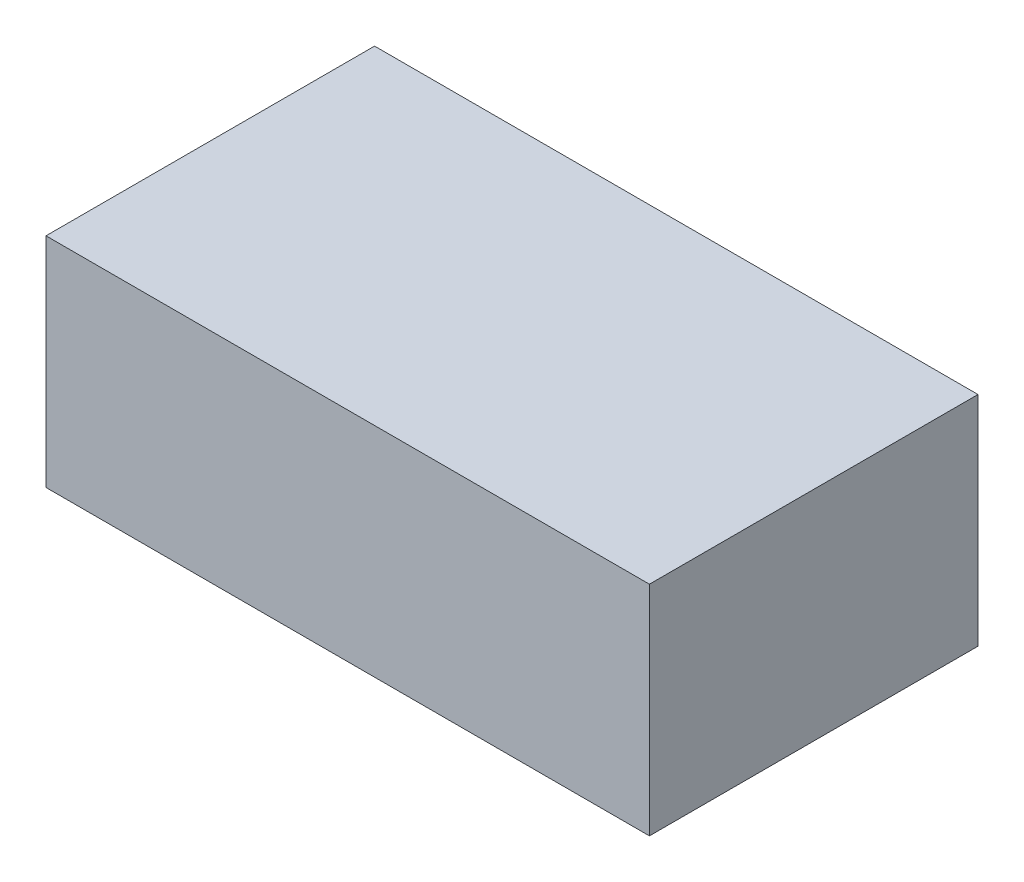
SolidWorks part; units mm, degrees
ref_plane "Front Plane" through (0, 0, 0) normal (0, 0, 1) x (1, 0, 0)
ref_plane "Top Plane" through (0, 0, 0) normal (0, 1, 0) x (1, 0, 0)
ref_plane "Right Plane" through (0, 0, 0) normal (1, 0, 0) x (0, 0, -1)
sketch "Sketch2" plane through (0, 0, 0) normal (0, 1, 0) x (1, 0, 0)
  line L1 (24.257, -13.208) -> (-24.257, -13.208)
  line L2 (24.257, -13.208) -> (24.257, 13.208)
  line L3 (24.257, 13.208) -> (-24.257, 13.208)
  line L4 (-24.257, -13.208) -> (-24.257, 13.208)
  line L5 (24.257, -13.208) -> (-24.257, 13.208) construction
  line L6 (24.257, 13.208) -> (-24.257, -13.208) construction
  point P0 (0, 0)
  dimension "D1" = 26.416
  dimension "D2" = 48.514
extrude "Boss-Extrude1" add sketch "Sketch2" along normal blind 17.526
